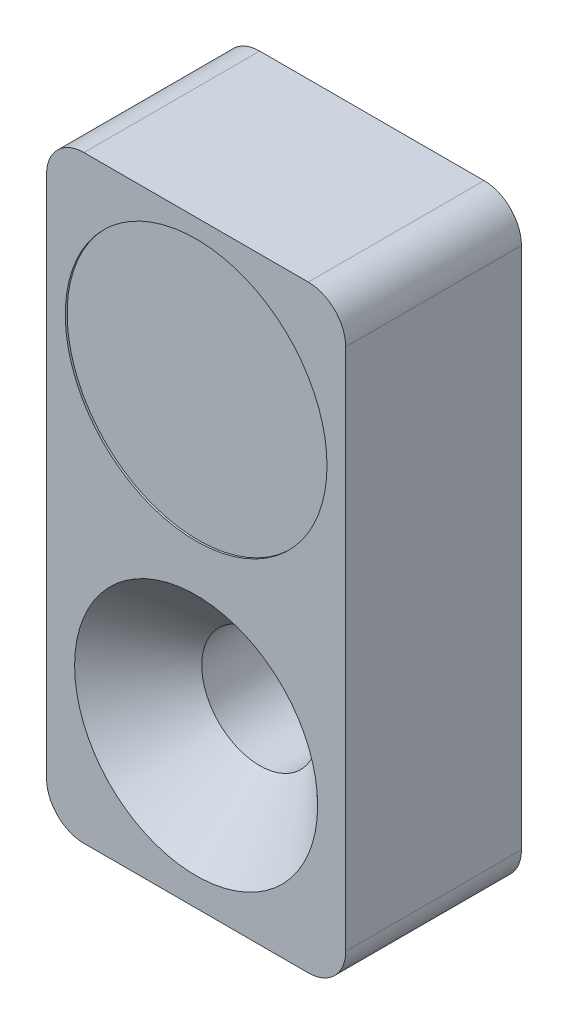
SolidWorks part; units mm, degrees
ref_plane "Vorne" through (0, 0, 0) normal (0, 0, 1) x (1, 0, 0)
ref_plane "Oben" through (0, 0, 0) normal (0, 1, 0) x (1, 0, 0)
ref_plane "Rechts" through (0, 0, 0) normal (1, 0, 0) x (0, 0, -1)
sketch "Skizze1" plane through (0, 0, 0) normal (0, 0, 1) x (1, 0, 0)
  line L1 (0, 0) -> (8, 0)
  line L2 (0, 0) -> (0, -16)
  line L3 (0, -16) -> (8, -16)
  line L4 (8, 0) -> (8, -16)
  dimension "D1" = 8
  dimension "D2" = 16
extrude "Aufsatz-Linear austragen1" add sketch "Skizze1" along normal blind 4.7
fillet "Verrundung1" radius 1 4 edges at (0, -16, 2.35) (8, -16, 2.35) (0, 0, 2.35) (8, 0, 2.35)
sketch "Skizze2" plane through (0, 0, 4.7) normal (0, 0, 1) x (1, 0, 0)
  line L0 (7, 0) -> (1, 0) construction
  line L1 (0, -1) -> (0, -15) construction
  circle A0 centre (4, -4) radius 3.5
  dimension "D2" = 7
  dimension "D1" = 4
  dimension "D3" = 4
extrude "Schnitt-Linear austragen1" cut sketch "Skizze2" against normal blind 0.05
ref_plane "Ebene1" through (4, 0, 0) normal (1, 0, 0) x (0, 0, -1)
sketch "Skizze3" plane through (4, 0, 0) normal (1, 0, 0) x (0, 0, -1)
  line L0 (-4.7, -12) -> (0, -12) construction
  line L1 (-4.7, -15) -> (-4.7, -1) construction
  line L2 (0, -15) -> (0, -1) construction
  line L3 (-4.7, -8.75) -> (-3, -10.45)
  line L4 (-3, -10.45) -> (0, -10.45)
  line L5 (0, -10.45) -> (0, -12)
  line L6 (0, -12) -> (-4.7, -12)
  line L7 (-4.7, -12) -> (-4.7, -8.75)
  dimension "D1" = 12
  dimension "D2" = 45
  dimension "D3" = 3.25
  dimension "D4" = 1.55
revolve "Schnitt-Rotation1" cut sketch "Skizze3" angle 360 about L0
move or copy body "Körper-Verschieben/Kopieren1" [suppressed] bodies to move or copy 105
